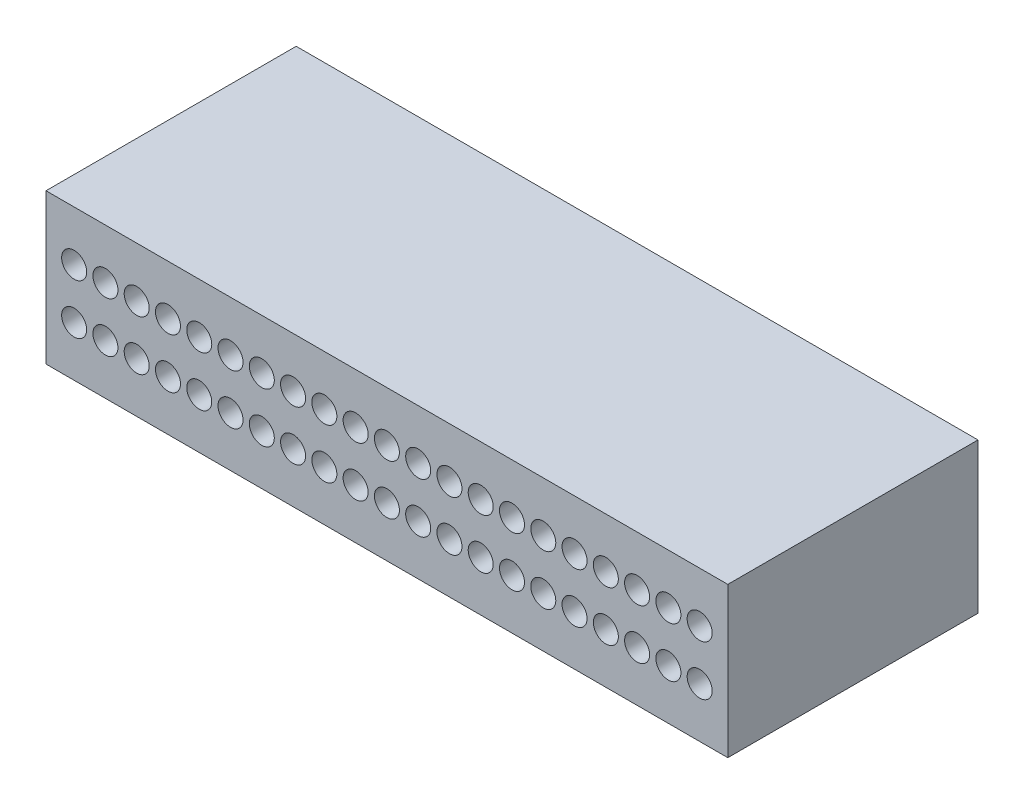
SolidWorks part; units mm, degrees
ref_plane "Front Plane" through (0, 0, 0) normal (0, 0, 1) x (1, 0, 0)
ref_plane "Top Plane" through (0, 0, 0) normal (0, 1, 0) x (1, 0, 0)
ref_plane "Right Plane" through (0, 0, 0) normal (1, 0, 0) x (0, 0, -1)
sketch "Sketch2" plane through (0, 0, 0) normal (0, 0, 1) x (1, 0, 0)
  line L1 (0, 0) -> (27.25, 0)
  line L2 (0, 0) -> (0, 6)
  line L3 (0, 6) -> (27.25, 6)
  line L4 (27.25, 0) -> (27.25, 6)
  dimension "D1" = 27.25
  dimension "D2" = 6
extrude "Boss-Extrude1" add sketch "Sketch2" along normal blind 10
sketch "Sketch3" plane through (0, 0, 10) normal (0, 0, 1) x (1, 0, 0)
  line L0 (0, 2) -> (27.25, 2) construction
  line L1 (0, 6) -> (0, 0) construction
  line L2 (27.25, 0) -> (27.25, 6) construction
  line L3 (0, 3) -> (27.25, 3) construction
  line L4 (27.25, 6) -> (0, 6) construction
  line L5 (0, 0) -> (27.25, 0) construction
  line L6 (1.125, 6) -> (1.125, 0) construction
  circle A0 centre (1.125, 2) radius 0.5
  circle A1 centre (2.375, 2) radius 0.5
  circle A2 centre (3.625, 2) radius 0.5
  circle A3 centre (4.875, 2) radius 0.5
  circle A4 centre (6.125, 2) radius 0.5
  circle A5 centre (7.375, 2) radius 0.5
  circle A6 centre (8.625, 2) radius 0.5
  circle A7 centre (9.875, 2) radius 0.5
  circle A8 centre (11.125, 2) radius 0.5
  circle A9 centre (12.375, 2) radius 0.5
  circle A10 centre (13.625, 2) radius 0.5
  circle A11 centre (14.875, 2) radius 0.5
  circle A12 centre (16.125, 2) radius 0.5
  circle A13 centre (17.375, 2) radius 0.5
  circle A14 centre (18.625, 2) radius 0.5
  circle A15 centre (19.875, 2) radius 0.5
  circle A16 centre (21.125, 2) radius 0.5
  circle A17 centre (22.375, 2) radius 0.5
  circle A18 centre (23.625, 2) radius 0.5
  circle A19 centre (24.875, 2) radius 0.5
  circle A20 centre (26.125, 2) radius 0.5
  dimension "D1" = 1
  dimension "D6" = 1
  dimension "D7" = 1.25
  dimension "D2" = 2
  dimension "D3" = 1.125
  dimension "D5" = 1.25
  dimension "D4" = 20
extrude "Cut-Extrude1" cut sketch "Sketch3" against normal blind 5
ref_plane "Plane1" through (0, 3, 0) normal (0, -1, 0) x (-1, 0, 0)
mirror "Mirror1" about plane through (0, 3, 0) normal (0, -1, 0) of "Cut-Extrude1"
sketch "Sketch5" plane through (0, 0, 10) normal (0, 0, 1) x (1, 0, 0)
  point P0 (1.125, 4)
  point P1 (2.375, 4)
  point P3 (3.625, 4)
  point P5 (4.875, 4)
  point P7 (6.125, 4)
  point P9 (7.375, 4)
  point P11 (8.625, 4)
  point P13 (9.875, 4)
  point P15 (11.125, 4)
  point P17 (12.375, 4)
  point P19 (13.625, 4)
  point P21 (14.875, 4)
  point P23 (16.125, 4)
  point P25 (17.375, 4)
  point P27 (18.625, 4)
  point P29 (19.875, 4)
  point P31 (21.125, 4)
  point P33 (22.375, 4)
  point P35 (23.625, 4)
  point P37 (24.875, 4)
  point P39 (24.875, 2)
  point P41 (23.625, 2)
  point P43 (22.375, 2)
  point P45 (21.125, 2)
  point P47 (19.875, 2)
  point P49 (18.625, 2)
  point P51 (17.375, 2)
  point P53 (16.125, 2)
  point P55 (14.875, 2)
  point P57 (13.625, 2)
  point P59 (12.375, 2)
  point P61 (11.125, 2)
  point P63 (9.875, 2)
  point P65 (8.625, 2)
  point P67 (7.375, 2)
  point P69 (6.125, 2)
  point P71 (4.875, 2)
  point P73 (3.625, 2)
  point P75 (2.375, 2)
  point P77 (1.125, 2)
  point P79 (26.125, 4)
  point P81 (26.125, 2)
